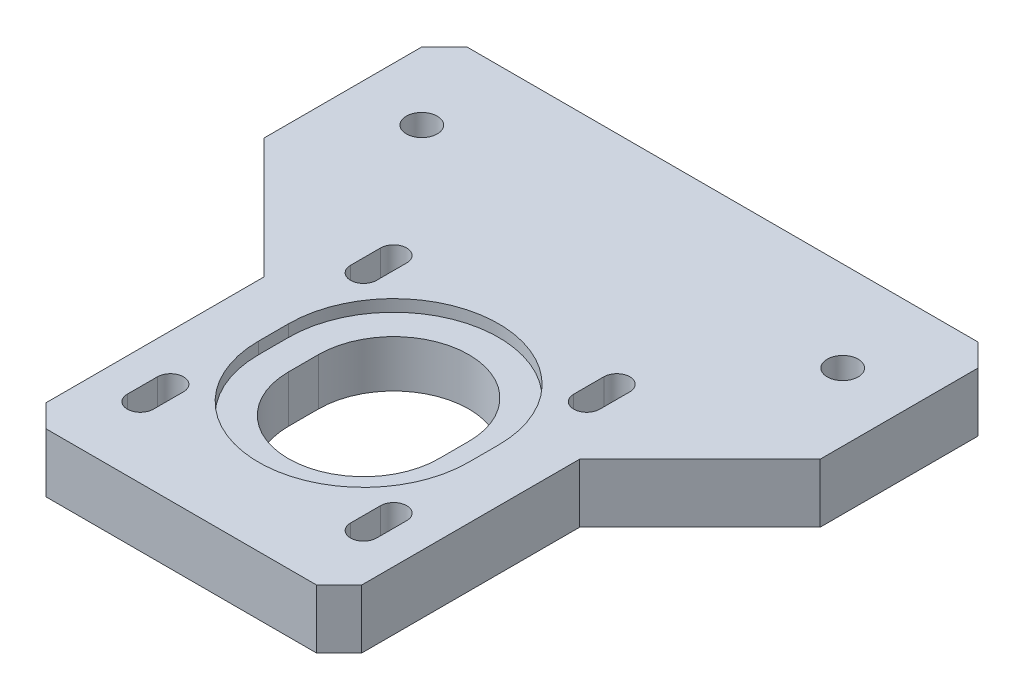
SolidWorks part; units mm, degrees
material "ASTM A36 Steel"
ref_plane "Front Plane" through (0, 0, 0) normal (0, 0, 1) x (1, 0, 0)
ref_plane "Top Plane" through (0, 0, 0) normal (0, 1, 0) x (1, 0, 0)
ref_plane "Right Plane" through (0, 0, 0) normal (1, 0, 0) x (0, 0, -1)
sketch "Sketch1" plane through (0, 0, 0) normal (0, 1, 0) x (1, 0, 0)
  line L0 (-33.3375, 57.15) -> (-58.7375, 57.15)
  line L1 (-33.3375, 57.15) -> (33.3375, 57.15)
  line L2 (-33.3375, 57.15) -> (-33.3375, -57.15) construction
  line L3 (-33.3375, -57.15) -> (33.3375, -57.15)
  line L4 (33.3375, 57.15) -> (33.3375, -57.15) construction
  line L5 (-33.3375, 57.15) -> (33.3375, -57.15) construction
  line L6 (-33.3375, -57.15) -> (33.3375, 57.15) construction
  line L7 (-58.7375, 57.15) -> (-58.7375, 19.05)
  line L8 (-58.7375, 19.05) -> (-33.3375, -6.35)
  line L9 (-33.3375, -6.35) -> (-33.3375, -57.15)
  line L10 (0, -57.15) -> (0, 57.15) construction
  line L11 (58.7375, 19.05) -> (33.3375, -6.35)
  line L12 (58.7375, 57.15) -> (58.7375, 19.05)
  line L13 (33.3375, 57.15) -> (58.7375, 57.15)
  line L14 (33.3375, -6.35) -> (33.3375, -57.15)
  point P0 (0, 0)
  dimension "D1" = 66.675
  dimension "D2" = 114.3
  dimension "D3" = 45
  dimension "D4" = 38.1
  dimension "D5" = 25.4
extrude "Boss-Extrude1" add sketch "Sketch1" along normal mid plane 12.7
hole_wizard "5/16-18 Tapped Hole1" positions "Sketch2" profile "Sketch3" tap size "5/16-18" standard "ANSI Inch" end condition through all
sketch "Sketch2" plane through (0, 6.35, 0) normal (0, 1, 0) x (1, 0, 0)
  line L0 (58.7375, 57.15) -> (-58.7375, 57.15) construction
  line L2 (44.45, 38.1) -> (58.7375, 38.1) construction
  line L5 (-44.45, 38.1) -> (-58.7375, 38.1) construction
  line L9 (58.7375, 19.05) -> (58.7375, 57.15) construction
  line L10 (-58.7375, 57.15) -> (-58.7375, 19.05) construction
  point P0 (-44.45, 38.1)
  point P2 (44.45, 38.1)
  point P27 (32.1923, 38.1)
  dimension "D1" = 19.05
  dimension "D2" = 88.9
sketch "Sketch3" plane through (-44.45, 6.35, -38.1) normal (1, 0, 0) x (0, 0, 1)
  line L0 (0, 0) -> (0, 12.7)
  line L1 (0, 12.7) -> (3.2639, 12.7)
  line L2 (3.2639, 12.7) -> (3.2639, 0)
  line L5 (3.2639, 0) -> (0, 0)
  line L11 (0, -6.35) -> (0, 107.95) construction
  dimension "Thru Tap Drill Dia." = 6.5278
  dimension "Thru Tap Drill Depth" = 12.7
sketch "Sketch4" plane through (0, 6.35, 0) normal (0, 1, 0) x (1, 0, 0)
  line L22 (33.3375, -57.15) -> (33.3375, -6.35)
  line L23 (33.3375, -6.35) -> (58.7375, 19.05)
  line L24 (58.7375, 19.05) -> (58.7375, 57.15)
  line L25 (58.7375, 57.15) -> (-58.7375, 57.15)
  line L26 (-58.7375, 57.15) -> (-58.7375, 19.05)
  line L27 (-58.7375, 19.05) -> (-33.3375, -6.35)
  line L28 (-33.3375, -6.35) -> (-33.3375, -57.15)
  line L29 (-33.3375, -57.15) -> (33.3375, -57.15)
  line L30 (33.3375, -57.15) -> (33.3375, -6.35)
  line L31 (33.3375, -6.35) -> (58.7375, 19.05)
  line L32 (58.7375, 19.05) -> (58.7375, 57.15)
  line L33 (58.7375, 57.15) -> (-58.7375, 57.15)
  line L34 (-58.7375, 57.15) -> (-58.7375, 19.05)
  line L35 (-58.7375, 19.05) -> (-33.3375, -6.35)
  line L36 (-33.3375, -6.35) -> (-33.3375, -57.15)
  line L37 (-33.3375, -57.15) -> (33.3375, -57.15)
  dimension "D1" = 0
extrude "Cut-Extrude1" cut sketch "Sketch4" against normal up to surface (0.25 mm away)
sketch "Sketch11" plane through (0, -6.35, 0) normal (0, -1, 0) x (1, 0, 0)
  circle A0 centre (-23.57, 35.87) radius 2.5 construction
  circle A1 centre (-23.57, -11.27) radius 2.5 construction
  circle A2 centre (23.57, -11.27) radius 2.5 construction
  circle A3 centre (23.57, 35.87) radius 2.5 construction
  circle A4 centre (-23.57, 35.87) radius 2.5
  circle A5 centre (-23.57, -11.27) radius 2.5
  circle A6 centre (23.57, -11.27) radius 2.5
  circle A7 centre (23.57, 35.87) radius 2.5
sketch "Sketch12" plane through (0, -6.35, 0) normal (0, -1, 0) x (1, 0, 0)
  line L0 (23.57, -4.92) -> (23.57, -11.27) construction
  line L1 (26.324, -4.92) -> (26.324, -11.27)
  line L2 (20.816, -4.92) -> (20.816, -11.27)
  line L3 (23.57, -11.27) -> (23.57, 35.87) construction
  line L4 (-23.57, -11.27) -> (-23.57, 35.87) construction
  line L5 (-23.57, 12.3) -> (23.57, 12.3) construction
  line L6 (23.57, 35.87) -> (23.57, 42.22) construction
  line L7 (20.816, 35.87) -> (20.816, 42.22)
  line L8 (26.324, 35.87) -> (26.324, 42.22)
  arc A0 (26.324, -4.92) -> (20.816, -4.92) centre (23.57, -4.92) ccw
  arc A1 (20.816, -11.27) -> (26.324, -11.27) centre (23.57, -11.27) ccw
  circle A3 centre (23.57, -11.27) radius 2.5 construction
  circle A4 centre (23.57, -11.27) radius 2.5 construction
  circle A5 centre (23.57, -11.27) radius 2.754 construction
  arc A6 (20.816, 35.87) -> (26.324, 35.87) centre (23.57, 35.87) ccw
  arc A7 (26.324, 42.22) -> (20.816, 42.22) centre (23.57, 42.22) ccw
  point P2 (23.57, -8.095)
  point P19 (23.57, 39.045)
  dimension "D2" = 6.35
extrude "Cut-Extrude5" cut sketch "Sketch12" against normal through all
sketch "Sketch13" plane through (0, -6.35, 0) normal (0, -1, 0) x (1, 0, 0)
  line L0 (23.57, -15.946) -> (23.57, -0.244) construction
  line L1 (19.07, -15.946) -> (19.07, -0.244)
  line L2 (28.07, -15.946) -> (28.07, -0.244)
  line L3 (23.57, 31.194) -> (23.57, 46.896) construction
  line L4 (19.07, 31.194) -> (19.07, 46.896)
  line L5 (28.07, 31.194) -> (28.07, 46.896)
  line L6 (23.57, -15.946) -> (23.57, -20.446) construction
  line L7 (20.816, -11.27) -> (23.57, -20.446) construction
  line L8 (20.816, -4.92) -> (23.57, 4.256) construction
  line L9 (23.57, 26.694) -> (20.816, 35.87) construction
  line L10 (23.57, 26.694) -> (23.57, 31.194) construction
  line L11 (20.816, 42.22) -> (23.57, 51.396) construction
  arc A0 (19.07, -15.946) -> (28.07, -15.946) centre (23.57, -15.946) ccw
  arc A1 (28.07, -0.244) -> (19.07, -0.244) centre (23.57, -0.244) ccw
  arc A2 (19.07, 31.194) -> (28.07, 31.194) centre (23.57, 31.194) ccw
  arc A3 (28.07, 46.896) -> (19.07, 46.896) centre (23.57, 46.896) ccw
  arc A5 (20.816, -11.27) -> (26.324, -11.27) centre (23.57, -11.27) ccw construction
  arc A6 (20.816, 35.87) -> (26.324, 35.87) centre (23.57, 35.87) ccw construction
  arc A7 (20.816, -11.27) -> (26.324, -11.27) centre (23.57, -11.27) ccw construction
  arc A8 (20.816, 35.87) -> (26.324, 35.87) centre (23.57, 35.87) ccw construction
  point P2 (23.57, -8.095)
  point P8 (23.57, 39.045)
  dimension "D1" = 9
  dimension "D2" = 9.176
extrude "Cut-Extrude6" cut sketch "Sketch13" against normal blind 5
mirror "Mirror1" about plane through (0, 0, 0) normal (1, 0, 0) of "Cut-Extrude6", "Cut-Extrude5"
sketch "Sketch8" plane through (0, 6.1, 0) normal (0, 1, 0) x (1, 0, 0)
  line L0 (0, -18.65) -> (0, -12.3) construction
  line L1 (-22.175, -18.65) -> (-22.175, -12.3)
  line L2 (22.175, -18.65) -> (22.175, -12.3)
  circle A0 centre (0, -12.3) radius 19 construction
  circle A1 centre (0, -12.3) radius 19 construction
  arc A2 (-22.175, -18.65) -> (22.175, -18.65) centre (0, -18.65) ccw
  arc A3 (22.175, -12.3) -> (-22.175, -12.3) centre (0, -12.3) ccw
  circle A4 centre (0, -12.3) radius 22.175
  circle A5 centre (0, -12.3) radius 22.175 construction
  point P5 (0, -15.475)
  point P14 (0, 9.875)
  dimension "D2" = 6.35
  dimension "D1" = 3.175
extrude "Cut-Extrude3" cut sketch "Sketch8" against normal offset from surface (2.5 mm away) 1
sketch "Sketch9" plane through (0, 3.6, 0) normal (0, 1, 0) x (1, 0, 0)
  line L0 (0, -18.65) -> (0, -12.3) construction
  line L1 (-15.875, -18.65) -> (-15.875, -12.3)
  line L2 (22.175, -18.65) -> (22.175, -12.3)
  line L3 (22.175, -18.65) -> (22.175, -12.3)
  line L4 (-22.175, -12.3) -> (-22.175, -18.65)
  line L5 (-22.175, -12.3) -> (-22.175, -18.65)
  line L6 (15.875, -18.65) -> (15.875, -12.3)
  circle A0 centre (0, -12.3) radius 15.875 construction
  arc A1 (-22.175, -18.65) -> (22.175, -18.65) centre (0, -18.65) ccw
  arc A3 (-15.875, -18.65) -> (15.875, -18.65) centre (0, -18.65) ccw
  arc A4 (15.875, -12.3) -> (-15.875, -12.3) centre (0, -12.3) ccw
  arc A5 (-22.175, -18.65) -> (22.175, -18.65) centre (0, -18.65) ccw
  arc A6 (22.175, -12.3) -> (-22.175, -12.3) centre (0, -12.3) ccw
  arc A7 (22.175, -12.3) -> (-22.175, -12.3) centre (0, -12.3) ccw
  point P9 (0, -15.475)
  dimension "D2" = 31.75
  dimension "D3" = 6.35
extrude "Cut-Extrude4" cut sketch "Sketch9" against normal through all contours L6 A4 L1 A3
chamfer "Chamfer1" distance 4.7625 angle 45 4 edges at (58.7375, -0.125, -57.15) (-58.7375, -0.125, -57.15) (-33.3375, -0.125, 57.15) (33.3375, -0.125, 57.15)
ref_plane "MountPlane" through (0, 0, -38.1) normal (0, 0, -1) x (-1, 0, 0)
equation "\"nut_width\"= 8mm"
equation "\"nut_radius\"= 4.588mm"
equation "\"nut_depth\"= 4mm"
equation "\"D1@Sketch13\"=\"nut_width\"+1mm"
equation "\"D1@Cut-Extrude6\"= \"nut_depth\" + 1mm"
equation "\"D2@Sketch13\"=\"nut_radius\"*2"
equation "\"slot_length\"= .25in"
equation "\"D2@Sketch12\"= \"slot_length\""
equation "\"D2@Sketch8\"=\"slot_length\""
equation "\"D3@Sketch9\"=\"slot_length\""
